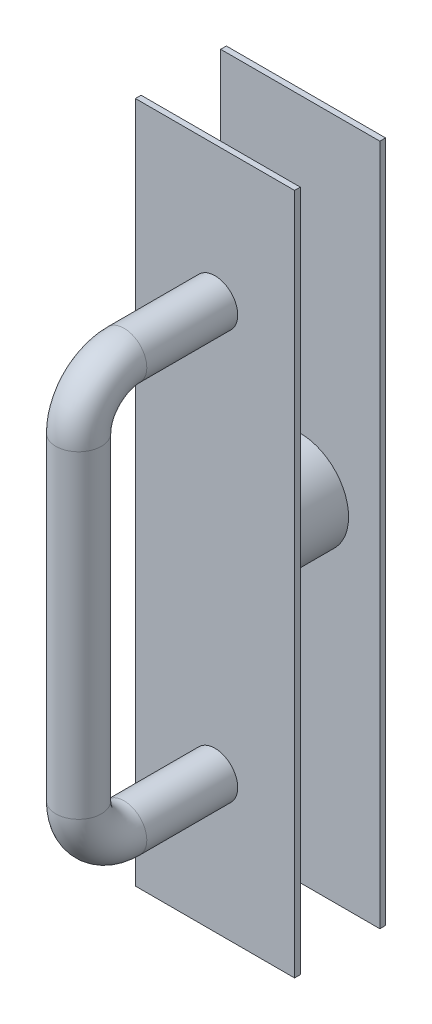
SolidWorks part; units mm, degrees
ref_plane "Front Plane" through (0, 0, 0) normal (0, 0, 1) x (1, 0, 0)
ref_plane "Top Plane" through (0, 0, 0) normal (0, 1, 0) x (1, 0, 0)
ref_plane "Right Plane" through (0, 0, 0) normal (1, 0, 0) x (0, 0, -1)
sketch "Sketch1" plane through (0, 0, 0) normal (0, 0, 1) x (1, 0, 0)
  circle A0 centre (0, 0) radius 26.9875
  dimension "D1" = 53.975
extrude "Boss-Extrude1" add sketch "Sketch1" against normal blind 44.45
sketch "Sketch2" plane through (0, 0, 0) normal (0, 0, 1) x (1, 0, 0)
  line L1 (-44.45, 190.5) -> (44.45, 190.5)
  line L2 (-44.45, 190.5) -> (-44.45, -190.5)
  line L3 (-44.45, -190.5) -> (44.45, -190.5)
  line L4 (44.45, 190.5) -> (44.45, -190.5)
  dimension "D1" = 88.9
  dimension "D2" = 381
  dimension "D3" = 44.45
  dimension "D4" = 190.5
extrude "Boss-Extrude2" add sketch "Sketch2" along normal blind 3.175
sketch "Sketch3" plane through (0, 0, 3.175) normal (0, 0, 1) x (1, 0, 0)
  line L0 (-44.45, -190.5) -> (44.45, -190.5) construction
  line L1 (44.45, -190.5) -> (44.45, 190.5) construction
  circle A0 centre (0, -114.3) radius 12.7
  dimension "D1" = 25.4
  dimension "D2" = 76.2
  dimension "D3" = 44.45
sketch "Sketch5" plane through (0, 0, 0) normal (1, 0, 0) x (0, 0, -1)
  line L0 (-3.175, -114.3) -> (-53.975, -114.3)
  line L1 (-3.175, -101.6) -> (-3.175, -127) construction
  line L2 (-79.375, -88.9) -> (-79.375, 88.9)
  line L3 (-53.975, 114.3) -> (-3.175, 114.3)
  line L4 (-3.175, -190.5) -> (-3.175, 190.5) construction
  arc A0 (-53.975, -114.3) -> (-79.375, -88.9) centre (-53.975, -88.9) cw
  arc A1 (-79.375, 88.9) -> (-53.975, 114.3) centre (-53.975, 88.9) cw
  dimension "D2" = 25.4
  dimension "D4" = 228.6
  dimension "D1" = 50.8
  dimension "D3" = 50.8
sweep "Sweep1" add profiles "Sketch3" path "Sketch5"
sketch "Sketch6" plane through (0, 0, -44.45) normal (0, 0, -1) x (-1, 0, 0)
  line L1 (44.45, 190.5) -> (-44.45, 190.5)
  line L2 (44.45, 190.5) -> (44.45, -190.5)
  line L3 (44.45, -190.5) -> (-44.45, -190.5)
  line L4 (-44.45, 190.5) -> (-44.45, -190.5)
  circle A0 centre (0, 0) radius 26.9875 construction
  dimension "D1" = 381
  dimension "D2" = 88.9
  dimension "D3" = 190.5
  dimension "D4" = 44.45
extrude "Boss-Extrude3" add sketch "Sketch6" along normal blind 3.175
